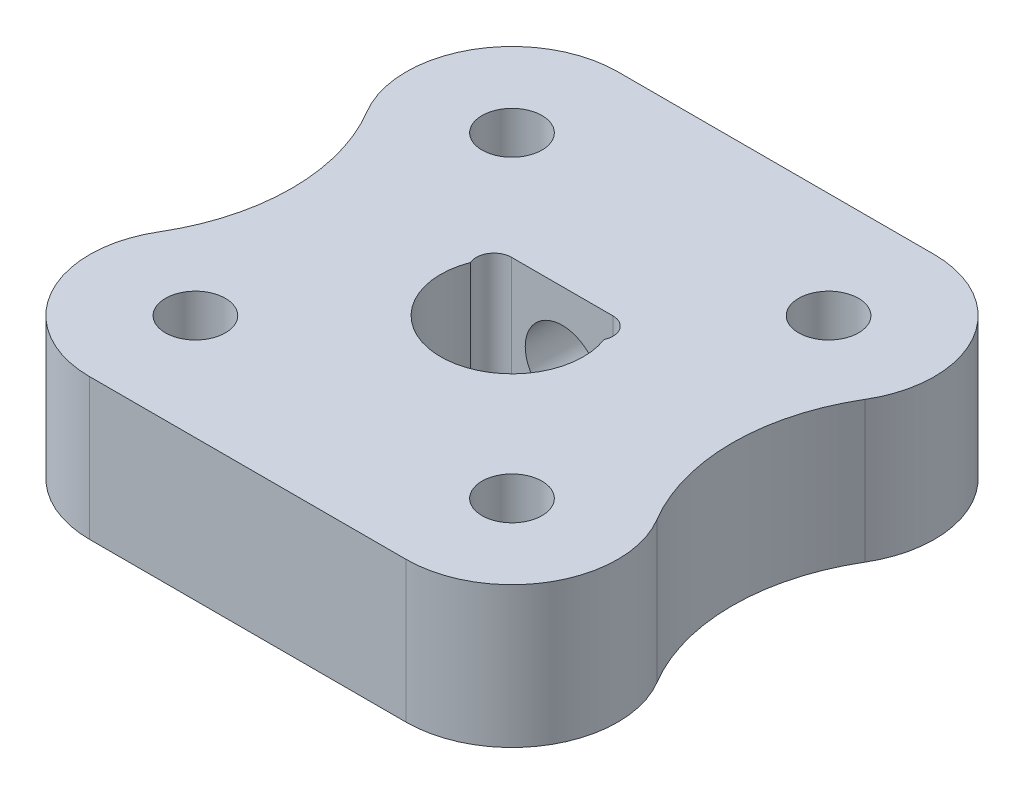
SolidWorks part; units mm, degrees
ref_plane "Front Plane" through (0, 0, 0) normal (0, 0, 1) x (1, 0, 0)
ref_plane "Top Plane" through (0, 0, 0) normal (0, 1, 0) x (1, 0, 0)
ref_plane "Right Plane" through (0, 0, 0) normal (1, 0, 0) x (0, 0, -1)
sketch "Sketch1" plane through (0, 0, 0) normal (0, 1, 0) x (1, 0, 0)
  line L0 (-9.35, 0) -> (9.35, 0) construction
  line L1 (0, 9.35) -> (0, -9.35) construction
  line L2 (0, 0) -> (6.6114, 6.6114) construction
  line L3 (-1.4387, 1.425) -> (1.4387, 1.425)
  line L4 (-1.4387, 1.425) -> (-1.4387, 0) construction
  line L5 (-4.4901, 7.4901) -> (4.4901, 7.4901)
  line L7 (-6.25, 0) -> (-6.25, -2.0605) construction
  line L8 (-4.4901, -7.4901) -> (4.4901, -7.4901)
  circle A0 centre (0, 0) radius 9.35
  circle A1 centre (0, 0) radius 2.025
  circle A2 centre (4.4901, 4.4901) radius 0.85
  circle A3 centre (-4.4901, 4.4901) radius 0.85
  circle A4 centre (4.4901, -4.4901) radius 0.85
  circle A5 centre (-4.4901, -4.4901) radius 0.85
  circle A6 centre (-1.4387, 0.925) radius 0.5
  circle A7 centre (1.4387, 0.925) radius 0.5
  circle A8 centre (-7.5, 0) radius 1.25
  circle A9 centre (-4.4901, 4.4901) radius 3
  circle A10 centre (-4.4901, -4.4901) radius 3
  arc A11 (-7.0649, -2.9504) -> (-7.0649, 2.9504) centre (-11.9988, 0) ccw
  arc A12 (7.0649, -2.9504) -> (7.0649, 2.9504) centre (11.9988, 0) cw
  circle A13 centre (4.4901, -4.4901) radius 3
  circle A14 centre (4.4901, 4.4901) radius 3
  point P19 (0, -2.025)
  dimension "D2" = 4.05
  dimension "D3" = 1.7
  dimension "D7" = 1
  dimension "D9" = 2.5
  dimension "D11" = 6
  dimension "D4" = 6.35
  dimension "D5" = 45
  dimension "D6" = 3.45
  dimension "D10" = 15
extrude "Base shape" add sketch "Sketch1" along normal blind 4
sketch "Sketch3" plane through (0, 0, -7.4901) normal (0, 0, 1) x (1, 0, 0)
  line L0 (-4.4901, 4) -> (4.4901, 0) construction
  circle A0 centre (0, 2) radius 1.05
  point P2 (0, 2)
  point P3 (-4.4901, 4)
  point P4 (4.4901, 0)
  dimension "D1" = 2.1
extrude "M2.5 Grub screw cut" cut sketch "Sketch3" along normal up to next
sketch "Main CS" plane through (0, 4, 0) normal (0, 1, 0) x (1, 0, 0)
  line L1 (-7.4901, 7.4901) -> (7.4901, 7.4901)
  line L2 (-7.4901, 7.4901) -> (-7.4901, -7.4901)
  line L3 (-7.4901, -7.4901) -> (7.4901, -7.4901)
  line L4 (7.4901, 7.4901) -> (7.4901, -7.4901)
  line L5 (-7.4901, 7.4901) -> (7.4901, -7.4901) construction
  line L6 (-7.4901, -7.4901) -> (7.4901, 7.4901) construction
  line L7 (-4.4901, -7.4901) -> (4.4901, -7.4901) construction
  arc A0 (-4.4901, 7.4901) -> (-7.0649, 2.9504) centre (-4.4901, 4.4901) ccw construction
  point P0 (0, 0)
  point P9 (0, 0)
  point P10 (7.4901, -7.4901)
sketch "Grub CS" plane through (0, 0, -7.4901) normal (0, 0, -1) x (-1, 0, 0)
  line L0 (-4.4901, 4) -> (4.4901, 0) construction
  line L1 (0, 2) -> (4.4901, 2) construction
  line L2 (4.4901, 4) -> (4.4901, 0) construction
  line L3 (0, 2) -> (0, 4) construction
  line L4 (4.4901, 4) -> (-4.4901, 4) construction
  point P4 (0, 2)
  point P10 (0, 0)
